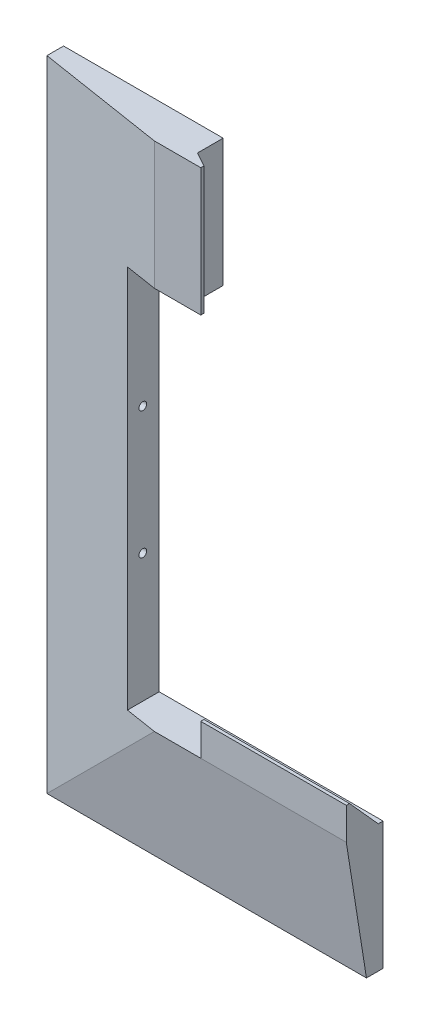
SolidWorks part; units mm, degrees
ref_plane "Płaszczyzna przednia" through (0, 0, 0) normal (0, 0, 1) x (1, 0, 0)
ref_plane "Płaszczyzna górna" through (0, 0, 0) normal (0, 1, 0) x (1, 0, 0)
ref_plane "Płaszczyzna prawa" through (0, 0, 0) normal (1, 0, 0) x (0, 0, -1)
sketch "Szkic2" plane through (0, 0, 0) normal (0, 0, 1) x (1, 0, 0)
  line L0 (18.5428, 83.2454) -> (18.5428, 43.3454)
  line L1 (-81.3572, 83.2454) -> (18.5428, 83.2454)
  line L2 (-81.3572, 83.2454) -> (-81.3572, -116.5546)
  line L3 (-81.3572, -116.5546) -> (18.5428, -116.5546)
  line L5 (-51.4572, 43.3454) -> (18.5428, 43.3454)
  line L6 (-51.4572, 43.3454) -> (-51.4572, -76.6546)
  line L7 (-51.4572, -76.6546) -> (18.5428, -76.6546)
  line L9 (-51.4572, -16.6546) -> (-81.3572, -16.6546) construction
  line L10 (18.5428, 43.3454) -> (18.5428, 83.2454) construction
  line L11 (18.5428, -76.6546) -> (18.5428, -116.5546) construction
  line L12 (18.5428, -76.6546) -> (18.5428, -116.5546)
  dimension "D1" = 199.8
  dimension "D3" = 120
  dimension "D4" = 29.9
extrude "Dodanie-wyciągnięcie1" add sketch "Szkic2" along normal blind 5.2
ref_plane "Płaszczyzna1" through (0, 0, 11.5) normal (0, 0, 1) x (1, 0, 0)
sketch "Szkic3" plane through (0, 0, 11.5) normal (0, 0, 1) x (1, 0, 0)
  line L5 (18.5428, -76.6546) -> (-51.4572, -76.6546) construction
  line L6 (-41.4572, -76.6546) -> (18.5428, -76.6546)
  line L12 (-41.4572, -76.6546) -> (-41.4572, 83.2454)
  line L13 (18.5428, 83.2454) -> (-81.3572, 83.2454) construction
  line L14 (-41.4572, 83.2454) -> (18.5428, 83.2454)
  line L15 (18.5428, 83.2454) -> (18.5428, -76.6546)
sketch "Szkic5" plane through (0, 0, 5.2) normal (0, 0, 1) x (1, 0, 0)
  line L1 (-81.3572, 83.2454) -> (18.5428, 83.2454)
  line L2 (-81.3572, 83.2454) -> (-81.3572, -116.5546)
  line L3 (-81.3572, -116.5546) -> (18.5428, -116.5546)
  line L4 (18.5428, 83.2454) -> (18.5428, -116.5546)
loft "Wyciągnięcie po profilach3" add profiles "Szkic3", "Szkic5"
sketch "Szkic6" plane through (-51.4572, 0, 0) normal (1, 0, 0) x (0, 0, -1)
  line L1 (0, 43.3454) -> (-49.2712, 43.3454)
  line L2 (0, 43.3454) -> (0, -76.6546)
  line L3 (0, -76.6546) -> (-49.2712, -76.6546)
  line L4 (-49.2712, 43.3454) -> (-49.2712, -76.6546)
extrude "Wytnij-wyciągnięcie1" cut sketch "Szkic6" along normal blind 78
sketch "Szkic7" plane through (-51.4572, 0, 0) normal (1, 0, 0) x (0, 0, -1)
  line L0 (-5.12, -76.6546) -> (-5.12, -36.5546) construction
  line L2 (-5.12, -36.5546) -> (-5.12, 3.2454) construction
  line L3 (-5.12, 3.2454) -> (-5.12, 43.3454) construction
  line L5 (0, -76.6546) -> (0, 43.3454) construction
  line L7 (-5.12, -34.1298) -> (-7.22, -35.3422)
  line L8 (-7.22, -35.3422) -> (-7.22, -37.7671)
  line L9 (-7.22, -37.7671) -> (-5.12, -38.9795)
  line L10 (-5.12, -38.9795) -> (-3.02, -37.7671)
  line L11 (-3.02, -37.7671) -> (-3.02, -35.3422)
  line L12 (-3.02, -35.3422) -> (-5.12, -34.1298)
  line L13 (-5.12, 5.6702) -> (-7.22, 4.4578)
  line L14 (-7.22, 4.4578) -> (-7.22, 2.0329)
  line L15 (-7.22, 2.0329) -> (-5.12, 0.8205)
  line L16 (-5.12, 0.8205) -> (-3.02, 2.0329)
  line L17 (-3.02, 2.0329) -> (-3.02, 4.4578)
  line L18 (-3.02, 4.4578) -> (-5.12, 5.6702)
  circle A0 centre (-5.12, -36.5546) radius 2.1 construction
  circle A1 centre (-5.12, 3.2454) radius 2.1 construction
  dimension "D2" = 4.2
  dimension "D3" = 4.2
  dimension "D1" = 5.12
extrude "Wytnij-wyciągnięcie2" cut sketch "Szkic7" against normal blind 5.6
sketch "Szkic9" plane through (-51.4572, 0, 0) normal (1, 0, 0) x (0, 0, -1)
  circle A0 centre (-5.12, 3.2454) radius 2.4249
  circle A1 centre (-5.12, -36.5546) radius 2.4249
  circle A2 centre (-5.12, 3.2454) radius 1.2
  circle A3 centre (-5.12, -36.5546) radius 1.2
extrude "Dodanie-wyciągnięcie3" add sketch "Szkic9" against normal blind 3.8
sketch "Szkic10" plane through (0, 0, 11.5) normal (0, 0, 1) x (1, 0, 0)
  line L0 (-41.4572, 83.2454) -> (-41.4572, 43.3454) construction
  line L1 (-31.4572, 83.2454) -> (18.5428, 83.2454)
  line L2 (-31.4572, 83.2454) -> (-31.4572, 43.3454)
  line L3 (-31.4572, 43.3454) -> (18.5428, 43.3454)
  line L4 (18.5428, 83.2454) -> (18.5428, 43.3454)
  dimension "D1" = 10
extrude "Wytnij-wyciągnięcie4" cut sketch "Szkic10" against normal blind 24
sketch "Szkic12" plane through (0, 83.2454, 0) normal (0, 1, 0) x (1, 0, 0)
  line L0 (-31.4572, -11.5) -> (-26.9572, -11.5)
  line L1 (-41.4572, -11.5) -> (18.5428, -11.5) construction
  line L2 (-26.9572, -11.5) -> (-26.9572, -10.5)
  line L3 (-26.9572, -10.5) -> (-31.4572, -8)
  line L4 (-31.4572, 0) -> (-31.4572, -11.5) construction
  line L5 (-31.4572, -8) -> (-31.4572, -11.5)
  point P5 (0, 0)
  point P10 (-26.7515, -10.3858)
extrude "Dodanie-wyciągnięcie4" add sketch "Szkic12" against normal blind 39.9
sketch "Szkic13" plane through (18.5428, 0, 0) normal (1, 0, 0) x (0, 0, -1)
  line L0 (-11.5, -76.6546) -> (-1.5, -76.6546)
  line L2 (-1.5, -76.6546) -> (-10.5, -66.6546)
  line L3 (-10.5, -66.6546) -> (-11.5, -66.6546)
  line L4 (-11.5, -66.6546) -> (-11.5, -76.6546)
  point P3 (-10.4274, -71.8305)
  point P5 (0, 0)
extrude "Dodanie-wyciągnięcie5" add sketch "Szkic13" against normal blind 45.5
